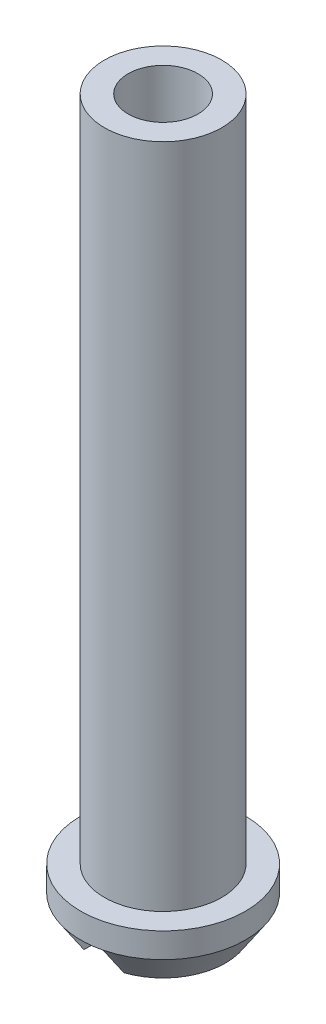
SolidWorks part; units mm, degrees
ref_plane "Plane1" through (0, 0, 0) normal (0, 0, 1) x (1, 0, 0)
ref_plane "Plane2" through (0, 0, 0) normal (0, 1, 0) x (1, 0, 0)
ref_plane "Plane3" through (0, 0, 0) normal (1, 0, 0) x (0, 0, -1)
sketch "Sketch1" plane through (0, 0, 0) normal (0, 0, 1) x (1, 0, 0)
  line L0 (0, 0) -> (0, 73.406) construction
  line L1 (3.556, 73.406) -> (3.556, 0)
  line L2 (3.556, 0) -> (6.35, 0)
  line L3 (6.35, 0) -> (8.382, 3.048)
  line L4 (8.382, 3.048) -> (8.382, 5.588)
  line L5 (8.382, 5.588) -> (5.969, 5.588)
  line L6 (5.969, 5.588) -> (5.969, 73.406)
  line L7 (5.969, 73.406) -> (3.556, 73.406)
  line L8 (-5.969, 73.406) -> (-3.556, 73.406) construction
  line L9 (-5.969, 5.588) -> (-5.969, 73.406) construction
  line L10 (-8.382, 5.588) -> (-5.969, 5.588) construction
  line L11 (-8.382, 3.048) -> (-8.382, 5.588) construction
  line L12 (-6.35, 0) -> (-8.382, 3.048) construction
  line L13 (-3.556, 0) -> (-6.35, 0) construction
  line L14 (-3.556, 73.406) -> (-3.556, 0) construction
  dimension "D1" = 73.406
  dimension "D2" = 5.588
  dimension "D3" = 11.938
  dimension "D4" = 16.764
  dimension "D5" = 7.112
  dimension "D6" = 2.54
  dimension "D7" = 12.7
revolve "Base-Revolve" add sketch "Sketch1" angle 360 about L0
chamfer "Chamfer2" distance 1.778 distance2 2.54 1 edges at (0, 0, -3.556)
sketch "Sketch2" plane through (0, 0, 0) normal (0, 0, 1) x (1, 0, 0)
  line L0 (-2.032, 0) -> (-2.032, 3.048)
  line L1 (-5.334, 0) -> (5.334, 0) construction
  line L2 (8.382, 3.048) -> (-8.382, 3.048) construction
  line L3 (2.032, 3.048) -> (2.032, 0)
  line L4 (2.032, 3.048) -> (-2.032, 3.048)
  line L5 (0, 0) -> (0, 2.54) construction
  line L6 (-6.35, 0) -> (6.35, 0) construction
  line L7 (-2.032, 0) -> (2.032, 0)
  dimension "D1" = 2.032
  dimension "D2" = 4.064
extrude "Cut-Extrude1" cut sketch "Sketch2" against normal through all and the other way through all
sketch "Sketch3" plane through (0, 0, 0) normal (0, 0, 1) x (1, 0, 0)
  line L0 (-7.874, 5.08) -> (-7.874, 2.286)
  line L4 (-8.382, 3.048) -> (-6.35, 0) construction
  line L5 (8.382, 3.048) -> (8.382, 5.588) construction
  line L6 (-7.874, 5.08) -> (-8.382, 5.08)
  line L7 (-8.382, 5.588) -> (-8.382, 3.048) construction
  line L8 (8.382, 5.588) -> (-8.382, 5.588) construction
  line L9 (-8.382, 3.048) -> (-7.874, 2.286)
  line L10 (-8.382, 5.08) -> (-8.382, 3.048)
  dimension "D1" = 16.256
  dimension "D2" = 0.508
extrude "Cut-Extrude2" cut sketch "Sketch3" against normal through all and the other way through all
